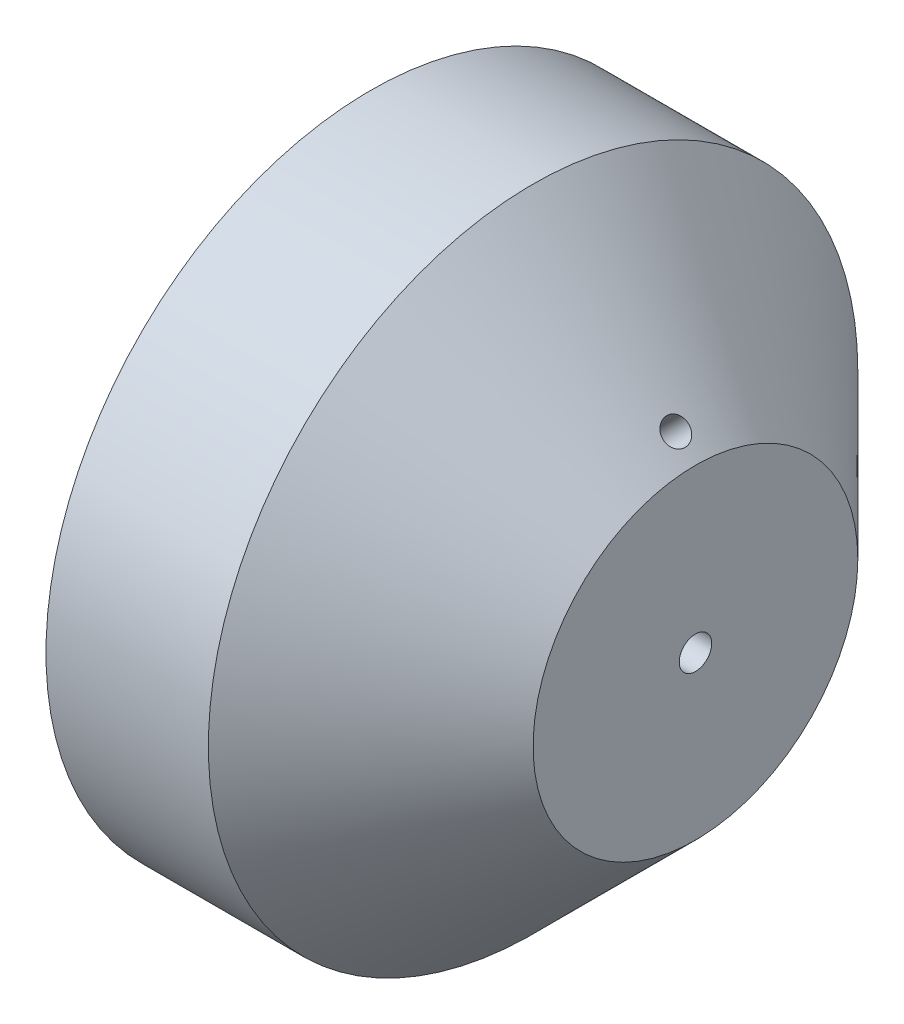
SolidWorks part; units mm, degrees
ref_plane "Vorderansicht-XY" through (0, 0, 0) normal (0, 0, 1) x (1, 0, 0)
ref_plane "Draufsicht-ZX" through (0, 0, 0) normal (0, 1, 0) x (1, 0, 0)
ref_plane "Seitenansicht-YZ" through (0, 0, 0) normal (1, 0, 0) x (0, 0, -1)
sketch "Skizze1" plane through (0, 0, 0) normal (1, 0, 0) x (0, 0, -1)
  circle A0 centre (0, 0) radius 50
  circle A1 centre (0, 0) radius 2.5
  dimension "D1" = 100
  dimension "D2" = 5
extrude "Aufsatz-Linear austragen1" add sketch "Skizze1" along normal blind 50
chamfer "Fase1" distance 25 angle 45 1 edges at (50, 0, -50)
hole_wizard "Ø4.0 (4) Durchmesser Bohrung1" positions "3D-Skizze1" profile "Skizze2" hole size "Ø4.0" standard "DIN"
sketch3d "3D-Skizze1"
  line L0 (50, 0, 0) -> (50, 37.5303, 0) construction
  line L1 (25, 0, 0) -> (50, 0, 0) construction
  point P0 (47, 28, 0)
  dimension "D1" = 3
sketch "Skizze2" plane through (47, 28, 0) normal (0, 0, 1) x (-0.7071, 0.7071, 0)
  line L0 (0, 0) -> (0, 36.0624)
  line L1 (0, 36.0624) -> (2, 36.0624)
  line L2 (2, 36.0624) -> (2, 0)
  line L5 (2, 0) -> (0, 0)
  line L11 (0, -6.35) -> (0, 107.95) construction
  dimension "Bohrerdurchmesser" = 4
  dimension "Bohrungstiefe" = 36.0624
ref_plane "Ebene1" through (37.5, 37.5, 0) normal (0.7071, 0.7071, 0) x (0.7071, -0.7071, 0)
